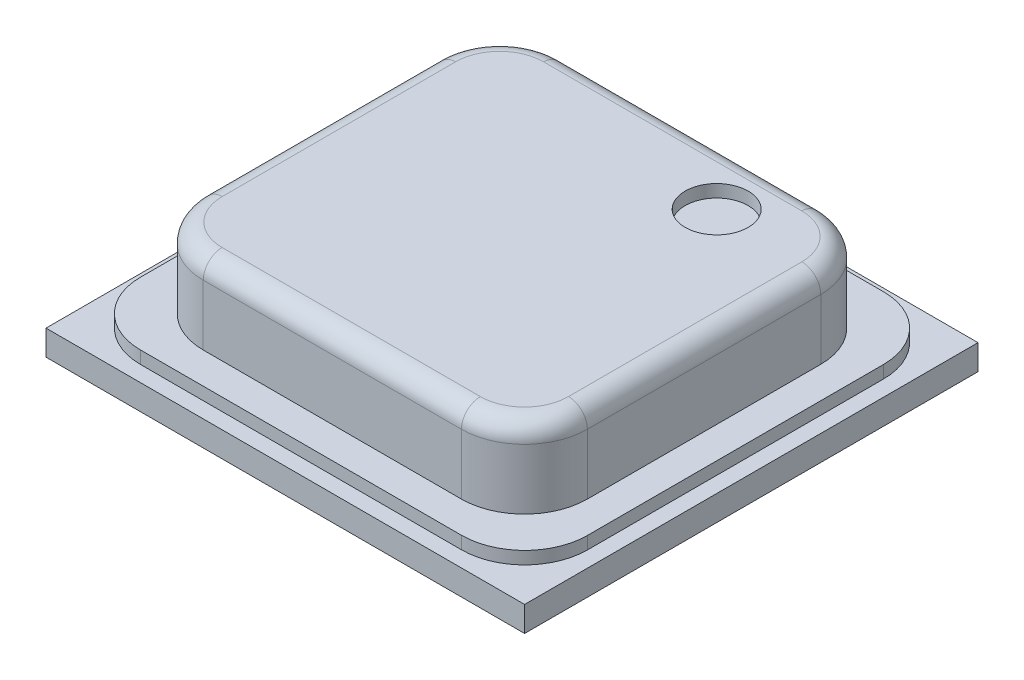
SolidWorks part; units mm, degrees
ref_plane "Front Plane" through (0, 0, 0) normal (0, 0, 1) x (1, 0, 0)
ref_plane "Top Plane" through (0, 0, 0) normal (0, 1, 0) x (1, 0, 0)
ref_plane "Right Plane" through (0, 0, 0) normal (1, 0, 0) x (0, 0, -1)
sketch "Sketch1" plane through (0, 0, 0) normal (0, 1, 0) x (1, 0, 0)
  line L1 (-1.9, 1.8) -> (1.9, 1.8)
  line L2 (-1.9, 1.8) -> (-1.9, -1.8)
  line L3 (-1.9, -1.8) -> (1.9, -1.8)
  line L4 (1.9, 1.8) -> (1.9, -1.8)
  line L5 (-1.9, 1.8) -> (1.9, -1.8) construction
  line L6 (-1.9, -1.8) -> (1.9, 1.8) construction
  point P0 (0, 0)
  dimension "D1" = 3.8
  dimension "D2" = 3.6
extrude "Boss-Extrude1" add sketch "Sketch1" along normal blind 0.2
sketch "Sketch2" plane through (0, 0.2, 0) normal (0, 1, 0) x (1, 0, 0)
  text T0 "BOTTOM" font "Century Gothic" height 1
sketch "Sketch3" plane through (0, 0.2, 0) normal (0, 1, 0) x (1, 0, 0)
  line L1 (-1.775, 1.675) -> (1.775, 1.675)
  line L2 (-1.775, 1.675) -> (-1.775, -1.675)
  line L3 (-1.775, -1.675) -> (1.775, -1.675)
  line L4 (1.775, 1.675) -> (1.775, -1.675)
  line L5 (-1.775, 1.675) -> (1.775, -1.675) construction
  line L6 (-1.775, -1.675) -> (1.775, 1.675) construction
  point P0 (0, 0)
  dimension "D1" = 3.55
  dimension "D2" = 3.35
extrude "Boss-Extrude2" add sketch "Sketch3" along normal blind 0.1
fillet "Fillet1" radius 0.5 4 edges at (1.775, 0.25, 1.675) (1.775, 0.25, -1.675) (-1.775, 0.25, -1.675) (-1.775, 0.25, 1.675)
sketch "Sketch4" plane through (0, 0.3, 0) normal (0, 1, 0) x (1, 0, 0)
  line L1 (-1.525, 1.4265) -> (1.525, 1.4265)
  line L2 (-1.525, 1.4265) -> (-1.525, -1.4265)
  line L3 (-1.525, -1.4265) -> (1.525, -1.4265)
  line L4 (1.525, 1.4265) -> (1.525, -1.4265)
  line L5 (-1.525, 1.4265) -> (1.525, -1.4265) construction
  line L6 (-1.525, -1.4265) -> (1.525, 1.4265) construction
  point P0 (0, 0)
  dimension "D1" = 3.05
  dimension "D2" = 2.853
extrude "Boss-Extrude3" add sketch "Sketch4" along normal blind 0.63
fillet "Fillet2" radius 0.5 4 edges at (1.525, 0.615, -1.4265) (1.525, 0.615, 1.4265) (-1.525, 0.615, -1.4265) (-1.525, 0.615, 1.4265)
fillet "Fillet5" radius 0.15 8 edges at (1.3786, 0.93, 1.2801) (0, 0.93, 1.4265) (-1.3786, 0.93, 1.2801) (-1.525, 0.93, 0) (-1.3786, 0.93, -1.2801) (0, 0.93, -1.4265) (1.3786, 0.93, -1.2801) (1.525, 0.93, 0)
sketch "Sketch5" plane through (0, 0.93, 0) normal (0, 1, 0) x (1, 0, 0)
  line L2 (1.9, 1.8) -> (-1.9, 1.8) construction
  line L3 (1.9, -1.8) -> (1.9, 1.8) construction
  circle A0 centre (0.675, 0.95) radius 0.25
  dimension "D1" = 0.5
  dimension "D2" = 0.85
  dimension "D3" = 1.225
extrude "Cut-Extrude1" cut sketch "Sketch5" against normal blind 0.1
